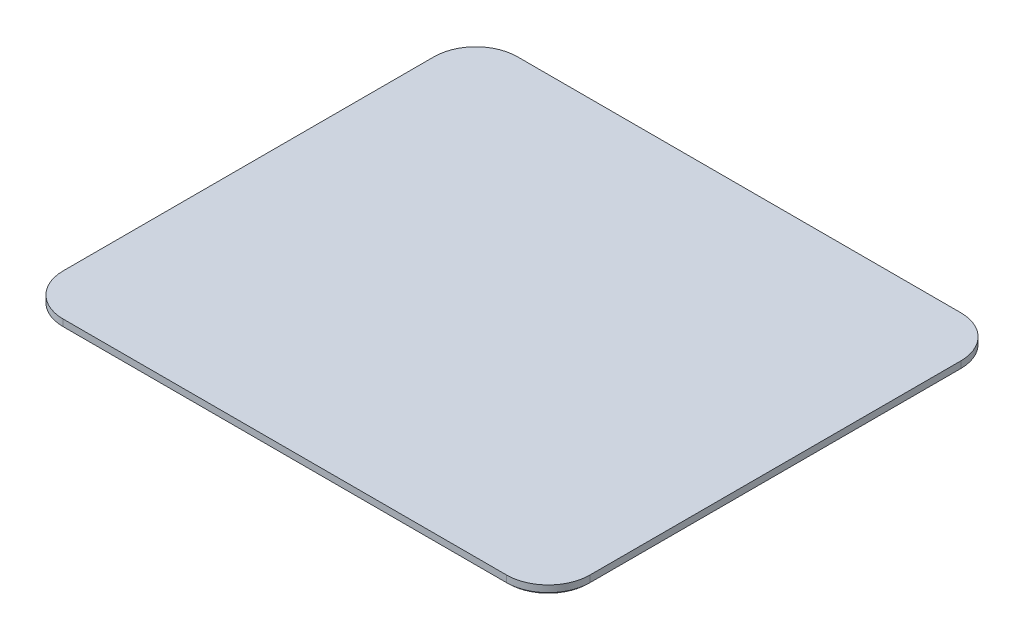
SolidWorks part; units mm, degrees
ref_plane "Front Plane" through (0, 0, 0) normal (0, 0, 1) x (1, 0, 0)
ref_plane "Top Plane" through (0, 0, 0) normal (0, 1, 0) x (1, 0, 0)
ref_plane "Right Plane" through (0, 0, 0) normal (1, 0, 0) x (0, 0, -1)
sketch "Sketch1" plane through (0, 0, 0) normal (0, 1, 0) x (1, 0, 0)
  line L1 (-266, 272.5) -> (266, 272.5)
  line L2 (-316, 222.5) -> (-316, -222.5)
  line L3 (-266, -272.5) -> (266, -272.5)
  line L4 (316, 222.5) -> (316, -222.5)
  line L5 (-316, 272.5) -> (316, -272.5) construction
  line L6 (-316, -272.5) -> (316, 272.5) construction
  arc A0 (-316, -222.5) -> (-266, -272.5) centre (-266, -222.5) ccw
  arc A1 (266, -272.5) -> (316, -222.5) centre (266, -222.5) ccw
  arc A2 (316, 222.5) -> (266, 272.5) centre (266, 222.5) ccw
  arc A3 (-266, 272.5) -> (-316, 222.5) centre (-266, 222.5) ccw
  point P0 (0, 0)
  dimension "D3" = 50
  dimension "D1" = 545
  dimension "D2" = 632
extrude "Boss-Extrude1" add sketch "Sketch1" along normal mid plane 10
chamfer "Chamfer1" distance 2 angle 45 8 edges at (301.3553, -5, 257.8553) (316, -5, 0) (301.3553, -5, -257.8553) (0, -5, -272.5) (-301.3553, -5, -257.8553) (-316, -5, 0) (-301.3553, -5, 257.8553) (0, -5, 272.5)
sketch "Sketch4" plane through (0, 5, 0) normal (0, 1, 0) x (1, 0, 0)
  line L0 (-100, 272.5) -> (100, 272.5)
  line L3 (266, 272.5) -> (-266, 272.5) construction
  line L6 (-100, 272.5) -> (-100, 262.5)
  line L7 (-100, 262.5) -> (100, 262.5)
  line L8 (100, 262.5) -> (100, 272.5)
extrude "Boss-Extrude3" add sketch "Sketch4" against normal blind 20
sketch "Sketch5" plane through (0, 0, 0) normal (1, 0, 0) x (0, 0, -1)
  line L0 (267.5, -15) -> (267.5, -14.9969)
  line L1 (262.5, -15) -> (272.5, -15) construction
  line L4 (262.5, -9.9969) -> (262.5, -15)
  line L5 (262.5, -15) -> (267.5, -15)
  arc A0 (262.5, -9.9969) -> (267.5, -14.9969) centre (267.5, -9.9969) ccw
  circle A1 centre (267.5, -9.9969) radius 2
extrude "Cut-Extrude1" cut sketch "Sketch5" against normal up to next and the other way up to next
sketch "Sketch6" plane through (0, -5, 0) normal (0, -1, 0) x (1, 0, 0)
  line L1 (-200, 200) -> (200, 200)
  line L2 (-250, 150) -> (-250, -150)
  line L3 (-200, -200) -> (200, -200)
  line L4 (250, 150) -> (250, -150)
  line L5 (-250, 200) -> (250, -200) construction
  line L6 (-250, -200) -> (250, 200) construction
  arc A0 (-200, 200) -> (-250, 150) centre (-200, 150) ccw
  arc A1 (-250, -150) -> (-200, -200) centre (-200, -150) ccw
  arc A2 (200, -200) -> (250, -150) centre (200, -150) ccw
  arc A3 (250, 150) -> (200, 200) centre (200, 150) ccw
  point P0 (0, 0)
  dimension "D3" = 50
  dimension "D1" = 500
  dimension "D2" = 400
extrude "Boss-Extrude4" add sketch "Sketch6" along normal blind 5
